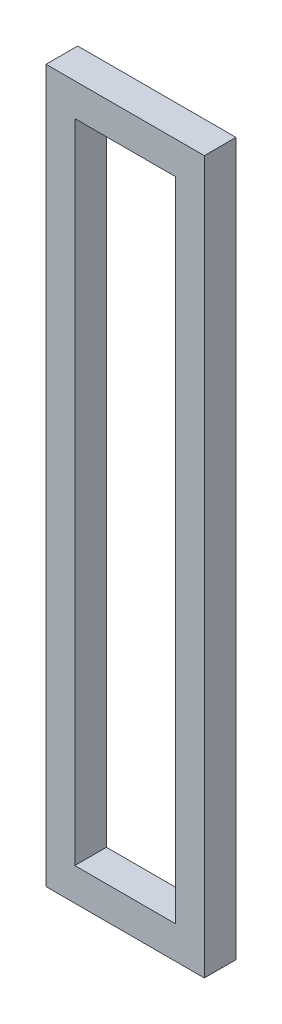
SolidWorks part; units mm, degrees
ref_plane "Front Plane" through (0, 0, 0) normal (0, 0, 1) x (1, 0, 0)
ref_plane "Top Plane" through (0, 0, 0) normal (0, 1, 0) x (1, 0, 0)
ref_plane "Right Plane" through (0, 0, 0) normal (1, 0, 0) x (0, 0, -1)
sketch "Sketch1" plane through (0, 0, 0) normal (0, 0, 1) x (1, 0, 0)
  line L1 (-50, -225) -> (50, -225)
  line L2 (-50, -225) -> (-50, 225)
  line L3 (-50, 225) -> (50, 225)
  line L4 (50, -225) -> (50, 225)
  line L5 (-50, -225) -> (50, 225) construction
  line L6 (-50, 225) -> (50, -225) construction
  point P0 (0, 0)
  dimension "D1" = 100
  dimension "D2" = 450
extrude "Boss-Extrude1" add sketch "Sketch1" along normal blind 20
sketch "Sketch2" plane through (0, 0, 20) normal (0, 0, 1) x (1, 0, 0)
  line L1 (-31.856, -204.4092) -> (31.856, -204.4092)
  line L2 (-31.856, -204.4092) -> (-31.856, 204.4092)
  line L3 (-31.856, 204.4092) -> (31.856, 204.4092)
  line L4 (31.856, -204.4092) -> (31.856, 204.4092)
  line L5 (-31.856, -204.4092) -> (31.856, 204.4092) construction
  line L6 (-31.856, 204.4092) -> (31.856, -204.4092) construction
  point P0 (0, 0)
extrude "Cut-Extrude1" cut sketch "Sketch2" against normal blind 68
